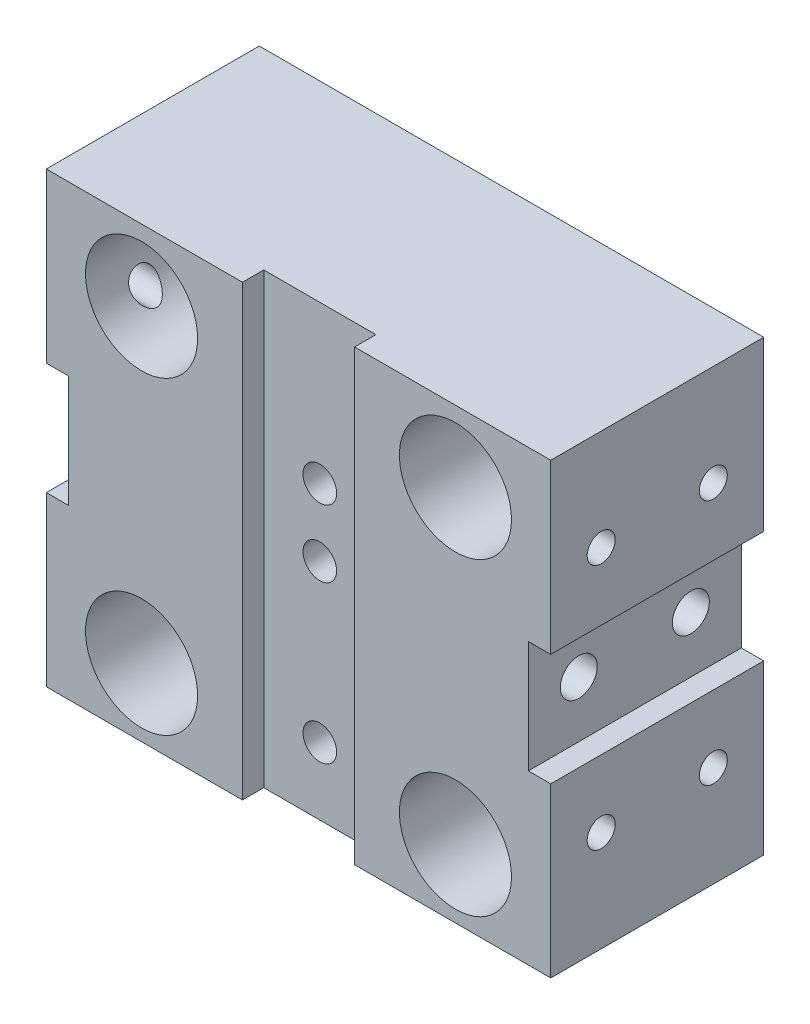
SolidWorks part; units mm, degrees
ref_plane "Front Plane" through (0, 0, 0) normal (0, 0, 1) x (1, 0, 0)
ref_plane "Top Plane" through (0, 0, 0) normal (0, 1, 0) x (1, 0, 0)
ref_plane "Right Plane" through (0, 0, 0) normal (1, 0, 0) x (0, 0, -1)
sketch "Sketch1" plane through (0, 0, 0) normal (0, 0, 1) x (1, 0, 0)
  line L0 (-19.5122, -12.3171) -> (-19.5122, -27.3171)
  line L1 (-19.5122, 12.6829) -> (25.4878, 12.6829)
  line L2 (-19.5122, 12.6829) -> (-19.5122, -2.3171)
  line L3 (-19.5122, -27.3171) -> (25.4878, -27.3171)
  line L4 (25.4878, 12.6829) -> (25.4878, -2.3171)
  line L5 (-19.5122, -2.3171) -> (-17.5122, -2.3171)
  line L6 (25.4878, -12.3171) -> (25.4878, -27.3171)
  line L7 (-19.5122, -12.3171) -> (-17.5122, -12.3171)
  line L8 (-17.5122, -2.3171) -> (-17.5122, -12.3171)
  line L9 (25.4878, -2.3171) -> (23.4878, -2.3171)
  line L11 (25.4878, -12.3171) -> (23.4878, -12.3171)
  line L12 (23.4878, -2.3171) -> (23.4878, -12.3171)
  dimension "D1" = 40
  dimension "D2" = 15
  dimension "D3" = 10
  dimension "D4" = 2
  dimension "D5" = 2
  dimension "D6" = 10
  dimension "D7" = 15
  dimension "D8" = 45
extrude "Boss-Extrude1" add sketch "Sketch1" along normal blind 19
sketch "Sketch2" plane through (0, 0, 19) normal (0, 0, 1) x (1, 0, 0)
  line L0 (25.4878, 12.6829) -> (-19.5122, 12.6829) construction
  line L1 (-2.0122, 12.6829) -> (7.9878, 12.6829)
  line L2 (-2.0122, 12.6829) -> (-2.0122, -27.3171)
  line L3 (-2.0122, -27.3171) -> (7.9878, -27.3171)
  line L4 (7.9878, 12.6829) -> (7.9878, -27.3171)
  line L5 (-19.5122, -27.3171) -> (25.4878, -27.3171) construction
  line L6 (-19.5122, 12.6829) -> (-19.5122, -2.3171) construction
  dimension "D1" = 17.5
  dimension "D2" = 10
extrude "Cut-Extrude1" cut sketch "Sketch2" against normal blind 1.9
sketch "Sketch3" plane through (0, 0, 19) normal (0, 0, 1) x (1, 0, 0)
  line L0 (-19.5122, 12.6829) -> (-19.5122, -2.3171) construction
  circle A0 centre (-11.0122, 6.3374) radius 5
  circle A1 centre (16.9878, 6.3374) radius 5
  circle A2 centre (-11.0122, -21.2515) radius 5
  circle A3 centre (16.9878, -21.2515) radius 5
  point P8 (0, 0)
  point P9 (0, 0)
  point P10 (0, 0)
  point P11 (0, 0)
  dimension "D1" = 10
  dimension "D2" = 8.5
  dimension "D3" = 36.5
extrude "Cut-Extrude2" cut sketch "Sketch3" against normal through all
sketch "Sketch4" plane through (0, 0, 0) normal (0, 0, -1) x (-1, 0, 0)
  line L0 (19.5122, -27.3171) -> (-25.4878, -27.3171) construction
  circle A0 centre (-2.9878, -19.3171) radius 4.25
  circle A1 centre (-2.9878, 4.6829) radius 4.25
  point P4 (0, 0)
  point P5 (0, 0)
  point P8 (-2.9878, -27.3171)
  dimension "D3" = 8.5
  dimension "D1" = 8
  dimension "D2" = 32
extrude "Cut-Extrude3" cut sketch "Sketch4" against normal blind 10
sketch "Sketch5" plane through (0, 0, 17.1) normal (0, 0, 1) x (1, 0, 0)
  line L0 (7.9878, 12.6829) -> (-2.0122, 12.6829) construction
  line L1 (-2.0122, -27.3171) -> (7.9878, -27.3171) construction
  circle A0 centre (2.9878, -1.3171) radius 1.5
  circle A1 centre (2.9878, -7.3171) radius 1.5
  circle A2 centre (2.9878, -21.3171) radius 1.5
  point P8 (2.9878, 12.6829)
  dimension "D1" = 3
  dimension "D2" = 6
  dimension "D3" = 20
  dimension "D4" = 26
extrude "Cut-Extrude4" cut sketch "Sketch5" against normal blind 10
hole_wizard "M3 Tapped Hole2" positions "Sketch8" profile "Sketch9" tap size "M3" standard "ISO"
sketch "Sketch8" plane through (-19.5122, 0, 0) normal (-1, 0, 0) x (0, 0, 1)
  line L0 (19, 12.6829) -> (0, 12.6829) construction
  line L1 (0, -12.3171) -> (0, -27.3171) construction
  line L2 (0, 12.6829) -> (0, -2.3171) construction
  point P0 (14.5, 3.6829)
  point P2 (4.5, 3.6829)
  point P4 (14.5, -18.3171)
  point P6 (4.5, -18.3171)
  dimension "D1" = 9
  dimension "D2" = 9
  dimension "D3" = 31
  dimension "D4" = 31
  dimension "D5" = 4.5
  dimension "D6" = 4.5
  dimension "D7" = 14.5
  dimension "D8" = 14.5
sketch "Sketch9" plane through (-19.5122, 3.6829, 14.5) normal (0, 1, 0) x (0, 0, 1)
  line L0 (0, 0) -> (0, 8.2511)
  line L1 (0, 8.2511) -> (1.25, 7.5)
  line L2 (1.25, 7.5) -> (1.25, 0)
  line L5 (1.25, 0) -> (0, 0)
  line L10 (0, 8.2511) -> (-1.25, 7.5) construction
  line L11 (0, -6.35) -> (0, 107.95) construction
  dimension "Tap Drill Dia." = 2.5
  dimension "Tap Drill Depth" = 7.5
  dimension "Drill Angle" = 118
cosmetic thread "Hole Thread5" parameters "D1"=6, "D2"=3
cosmetic thread "Hole Thread6" parameters "D1"=6, "D2"=3
cosmetic thread "Hole Thread7" parameters "D1"=6, "D2"=3
cosmetic thread "Hole Thread8" parameters "D1"=6, "D2"=3
hole_wizard "M4 Tapped Hole1" positions "Sketch10" profile "Sketch11" tap size "M4" standard "ISO"
sketch "Sketch10" plane through (-17.5122, 0, 0) normal (-1, 0, 0) x (0, 0, 1)
  line L0 (19, -2.3171) -> (19, -12.3171) construction
  line L1 (0, -2.3171) -> (0, -12.3171) construction
  point P0 (14.5, -7.3171)
  point P2 (4.5, -7.3171)
  point P7 (19, -7.3171)
  point P8 (0, 0)
  dimension "D1" = 14.5
  dimension "D2" = 4.5
sketch "Sketch11" plane through (-17.5122, -7.3171, 14.5) normal (0, 1, 0) x (0, 0, 1)
  line L0 (0, 0) -> (0, 11.0914)
  line L1 (0, 11.0914) -> (1.65, 10.1)
  line L2 (1.65, 10.1) -> (1.65, 0)
  line L5 (1.65, 0) -> (0, 0)
  line L10 (0, 11.0914) -> (-1.65, 10.1) construction
  line L11 (0, -6.35) -> (0, 107.95) construction
  dimension "Tap Drill Dia." = 3.3
  dimension "Tap Drill Depth" = 10.1
  dimension "Drill Angle" = 118
cosmetic thread "Hole Thread9" parameters "D1"=8, "D2"=4
cosmetic thread "Hole Thread10" parameters "D1"=8, "D2"=4
hole_wizard "M4 Tapped Hole2" positions "Sketch12" profile "Sketch13" tap size "M4" standard "ISO"
sketch "Sketch12" plane through (23.4878, 0, 0) normal (1, 0, 0) x (0, 0, -1)
  line L0 (0, -12.3171) -> (0, -2.3171) construction
  line L1 (-19, -27.3171) -> (0, -27.3171) construction
  point P0 (-14.5, -7.3171)
  point P2 (-4.5, -7.3171)
  dimension "D1" = 14.5
  dimension "D2" = 4.5
  dimension "D3" = 20
  dimension "D4" = 20
sketch "Sketch13" plane through (23.4878, -7.3171, 14.5) normal (0, 1, 0) x (0, 0, -1)
  line L0 (0, 0) -> (0, 11.0914)
  line L1 (0, 11.0914) -> (1.65, 10.1)
  line L2 (1.65, 10.1) -> (1.65, 0)
  line L5 (1.65, 0) -> (0, 0)
  line L10 (0, 11.0914) -> (-1.65, 10.1) construction
  line L11 (0, -6.35) -> (0, 107.95) construction
  dimension "Tap Drill Dia." = 3.3
  dimension "Tap Drill Depth" = 10.1
  dimension "Drill Angle" = 118
cosmetic thread "Hole Thread11" parameters "D1"=8, "D2"=4
cosmetic thread "Hole Thread12" parameters "D1"=8, "D2"=4
hole_wizard "M3 Tapped Hole3" positions "Sketch14" profile "Sketch15" tap size "M3" standard "ISO"
sketch "Sketch14" plane through (25.4878, 0, 0) normal (1, 0, 0) x (0, 0, -1)
  line L0 (0, -27.3171) -> (0, -12.3171) construction
  line L1 (0, -2.3171) -> (0, 12.6829) construction
  line L2 (-19, -27.3171) -> (0, -27.3171) construction
  line L3 (-19, -27.3171) -> (-19, -12.3171) construction
  line L4 (-19, -2.3171) -> (-19, 12.6829) construction
  point P0 (-14.5, -18.3171)
  point P2 (-4.5, -18.3171)
  point P4 (-4.5, 3.6829)
  point P6 (-14.5, 3.6829)
  dimension "D1" = 4.5
  dimension "D2" = 4.5
  dimension "D3" = 9
  dimension "D4" = 31
  dimension "D5" = 9
  dimension "D6" = 31
  dimension "D7" = 4.5
  dimension "D8" = 4.5
sketch "Sketch15" plane through (25.4878, -18.3171, 14.5) normal (0, 1, 0) x (0, 0, -1)
  line L0 (0, 0) -> (0, 8.2511)
  line L1 (0, 8.2511) -> (1.25, 7.5)
  line L2 (1.25, 7.5) -> (1.25, 0)
  line L5 (1.25, 0) -> (0, 0)
  line L10 (0, 8.2511) -> (-1.25, 7.5) construction
  line L11 (0, -6.35) -> (0, 107.95) construction
  dimension "Tap Drill Dia." = 2.5
  dimension "Tap Drill Depth" = 7.5
  dimension "Drill Angle" = 118
cosmetic thread "Hole Thread13" parameters "D1"=5.5515, "D2"=3
cosmetic thread "Hole Thread14" parameters "D1"=5.5515, "D2"=3
cosmetic thread "Hole Thread15" parameters "D1"=5.8344, "D2"=3
cosmetic thread "Hole Thread16" parameters "D1"=5.8344, "D2"=3
